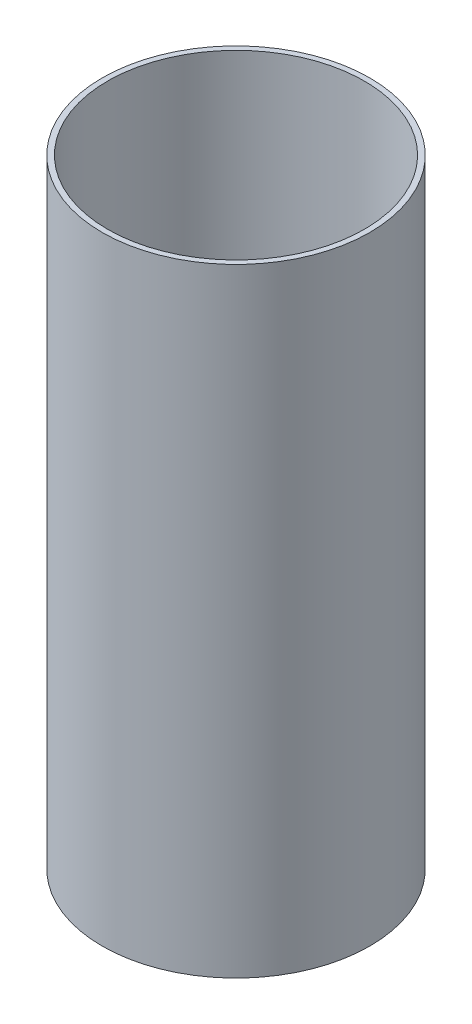
SolidWorks part; units mm, degrees
ref_plane "Front Plane" through (0, 0, 0) normal (0, 0, 1) x (1, 0, 0)
ref_plane "Top Plane" through (0, 0, 0) normal (0, 1, 0) x (1, 0, 0)
ref_plane "Right Plane" through (0, 0, 0) normal (1, 0, 0) x (0, 0, -1)
sketch "Sketch1" plane through (0, 0, 0) normal (0, 1, 0) x (1, 0, 0)
  circle A0 centre (0, 0) radius 47.498
  circle A1 centre (0, 0) radius 49.5046
  dimension "D1" = 94.996
  dimension "D2" = 99.0092
extrude "Boss-Extrude1" add sketch "Sketch1" along normal blind 228.6
